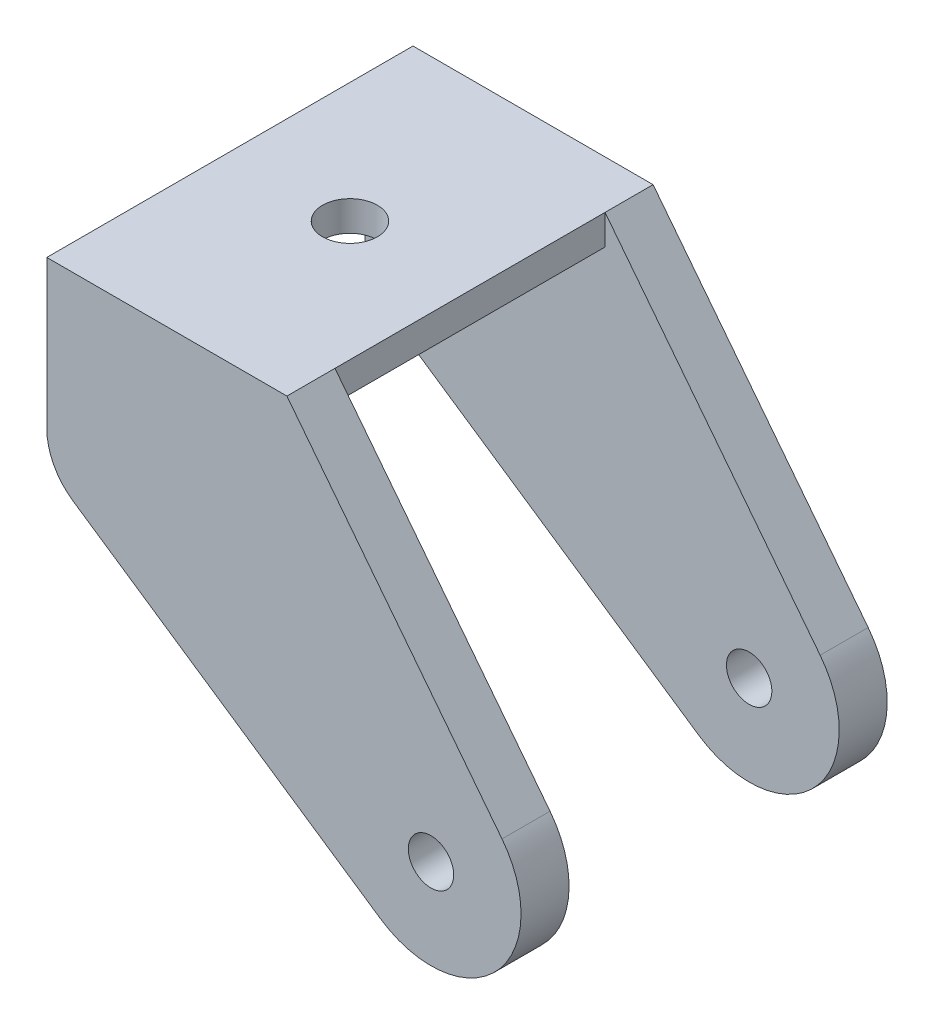
SolidWorks part; units mm, degrees
ref_plane "Front Plane" through (0, 0, 0) normal (0, 0, 1) x (1, 0, 0)
ref_plane "Top Plane" through (0, 0, 0) normal (0, 1, 0) x (1, 0, 0)
ref_plane "Right Plane" through (0, 0, 0) normal (1, 0, 0) x (0, 0, -1)
sketch "Sketch1" plane through (0, 0, 0) normal (0, 0, 1) x (1, 0, 0)
  line L0 (-40.64, 16.002) -> (-5.3385, -7.8884)
  line L1 (-40.64, 35.052) -> (-15.24, 35.052)
  line L2 (-40.64, 35.052) -> (-40.64, 16.002)
  line L3 (-40.64, 16.002) -> (-15.24, 16.002)
  line L4 (-15.24, 35.052) -> (-15.24, 16.002)
  line L5 (-15.24, 35.052) -> (7.5131, 5.8549)
  line L6 (-25.4, 0) -> (-25.4, 76.2) construction
  circle A0 centre (0, 0) radius 25.4 construction
  circle A1 centre (0, 0) radius 9.525
  dimension "D1" = 50.8
  dimension "D2" = 19.05
  dimension "D4" = 35.052
  dimension "D3" = 25.4
  dimension "D5" = 19.05
  dimension "D6" = 10.16
extrude "Boss-Extrude1" add sketch "Sketch1" along normal blind 5.08 contours L4 L1 L2 L3 | A1 L5 L4 L3 L0 | A1
hole_wizard "M4 Clearance Hole1" positions "Sketch2" profile "Sketch3" hole size "M4" standard "ANSI Metric" end condition through all
sketch "Sketch2" plane through (0, 0, 0) normal (0, 0, -1) x (-1, 0, 0)
  point P0 (0, 0)
sketch "Sketch3" plane through (0, 0, 0) normal (1, 0, 0) x (0, 1, 0)
  line L0 (0, 0) -> (0, 5.08)
  line L1 (0, 5.08) -> (2.4, 5.08)
  line L2 (2.4, 5.08) -> (2.4, 0)
  line L5 (2.4, 0) -> (0, 0)
  line L11 (0, -6.35) -> (0, 107.95) construction
  dimension "Thru Hole Dia." = 4.8
  dimension "Thru Hole Depth" = 5.08
sketch "Sketch4" plane through (0, 0, 5.08) normal (0, 0, 1) x (1, 0, 0)
  line L1 (-40.64, 35.052) -> (-15.24, 35.052)
  line L2 (-40.64, 35.052) -> (-40.64, 31.877)
  line L3 (-40.64, 31.877) -> (-15.24, 31.877)
  line L4 (-15.24, 35.052) -> (-15.24, 31.877)
  dimension "D1" = 3.175
extrude "Boss-Extrude2" add sketch "Sketch4" along normal blind 14.2875
mirror "Mirror3" about plane through (0, 0, 19.3675) normal (0, 0, 1) of bodies 103
hole_wizard "M5 Clearance Hole1" positions "Sketch5" profile "Sketch6" hole size "M5" standard "ANSI Metric" end condition through all
sketch "Sketch5" plane through (0, 35.052, 0) normal (0, 1, 0) x (1, 0, 0)
  line L0 (-40.64, -38.735) -> (-15.24, -38.735) construction
  line L1 (-40.64, -38.735) -> (-40.64, 0) construction
  point P0 (-27.94, -19.3675)
  point P5 (-27.94, -38.735)
  point P9 (-40.64, -19.3675)
sketch "Sketch6" plane through (-27.94, 35.052, 19.3675) normal (1, 0, 0) x (0, 0, 1)
  line L0 (0, 0) -> (0, 44.577)
  line L1 (0, 44.577) -> (2.9, 44.577)
  line L2 (2.9, 44.577) -> (2.9, 0)
  line L5 (2.9, 0) -> (0, 0)
  line L11 (0, -6.35) -> (0, 107.95) construction
  dimension "Thru Hole Dia." = 5.8
  dimension "Thru Hole Depth" = 44.577
fillet "Fillet1" radius 6.35 2 edges at (-40.64, 16.002, 2.54) (-40.64, 16.002, 36.195)
